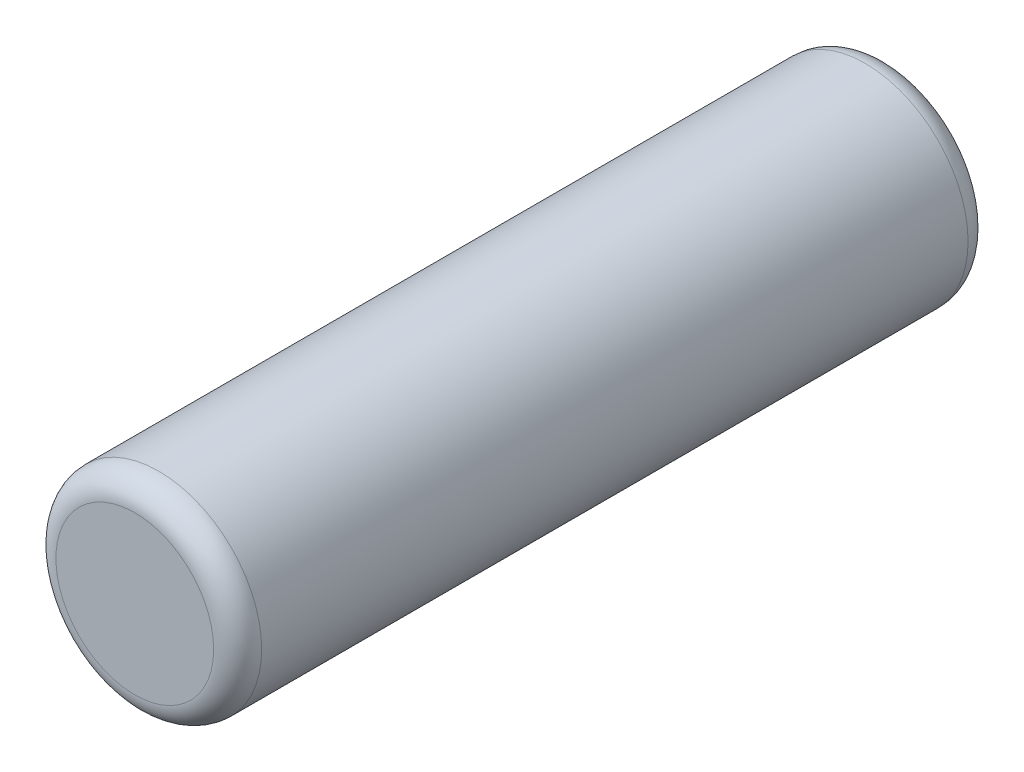
SolidWorks part; units mm, degrees
ref_plane "Front" through (0, 0, 0) normal (0, 0, 1) x (1, 0, 0)
ref_plane "Top" through (0, 0, 0) normal (0, 1, 0) x (1, 0, 0)
ref_plane "Right" through (0, 0, 0) normal (1, 0, 0) x (0, 0, -1)
sketch "Sketch1" plane through (0, 0, 0) normal (0, 0, 1) x (1, 0, 0)
  circle A0 centre (0, 0) radius 1.5
  dimension "D1" = 3
extrude "Boss-Extrude1" add sketch "Sketch1" along normal mid plane 11
fillet "Fillet1" radius 0.35 2 edges at (1.5, 0, -5.5) (1.5, 0, 5.5)
